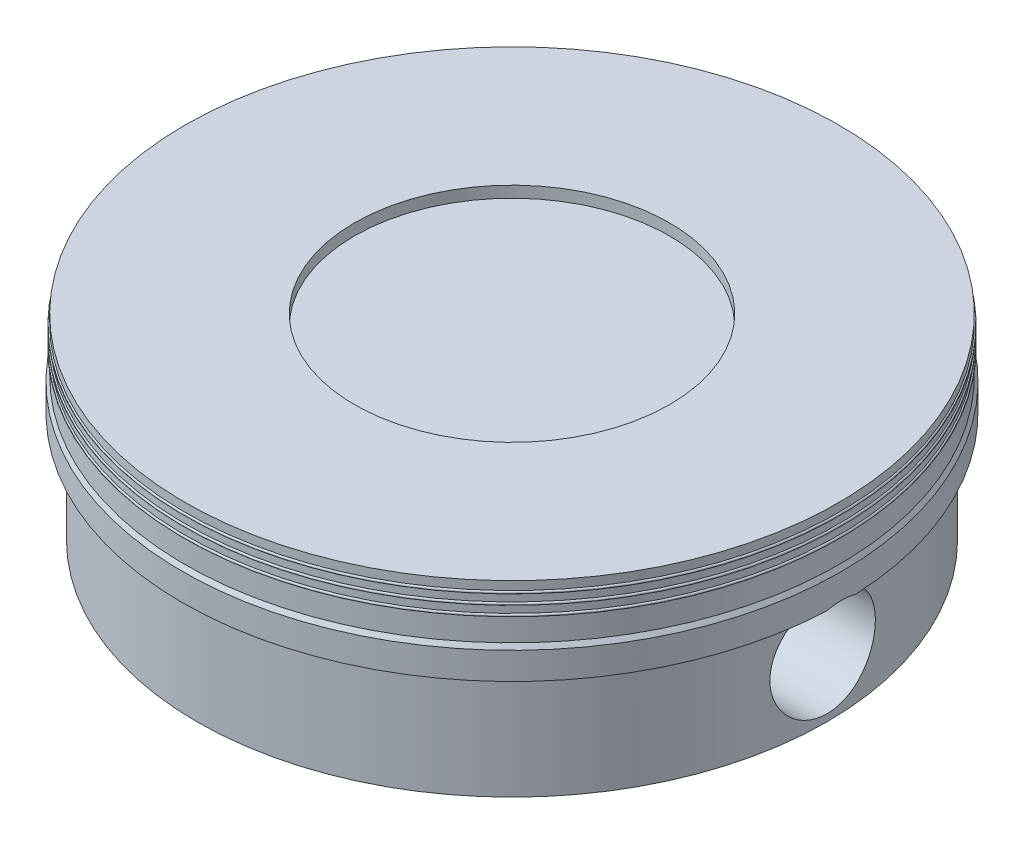
SolidWorks part; units mm, degrees
ref_plane "Front Plane" through (0, 0, 0) normal (0, 0, 1) x (1, 0, 0)
ref_plane "Top Plane" through (0, 0, 0) normal (0, 1, 0) x (1, 0, 0)
ref_plane "Right Plane" through (0, 0, 0) normal (1, 0, 0) x (0, 0, -1)
sketch "Sketch1" plane through (0, 0, 0) normal (0, 0, 1) x (1, 0, 0)
  line L0 (0, 3) -> (0, 0) construction
  line L1 (0, 0) -> (5, 0) construction
  line L2 (4.78, 0) -> (3.43, 0)
  line L3 (3.43, 0) -> (3.43, 1.93)
  line L4 (3.43, 1.93) -> (4.2, 1.93)
  line L5 (4.2, 1.93) -> (4.2, 2.33)
  line L6 (4.2, 2.33) -> (0, 2.33)
  line L7 (0, 2.33) -> (0, 2.8)
  line L8 (0, 2.8) -> (2.39, 2.8)
  line L9 (2.39, 2.8) -> (2.39, 2.972)
  line L10 (2.39, 2.972) -> (4.96, 2.972)
  line L11 (4.96, 2.972) -> (4.96, 2.842)
  line L12 (4.96, 2.155) -> (5, 2.085)
  line L13 (5, 2.085) -> (5, 1.675)
  line L14 (5, 1.675) -> (4.78, 1.675)
  line L15 (4.78, 1.675) -> (4.78, 0)
  line L16 (4.96, 2.802) -> (4.96, 2.692)
  line L17 (4.96, 2.652) -> (4.96, 2.542)
  line L18 (4.96, 2.502) -> (4.96, 2.155)
  arc A0 (4.96, 2.802) -> (4.96, 2.842) centre (4.96, 2.822) ccw
  arc A1 (4.96, 2.652) -> (4.96, 2.692) centre (4.96, 2.672) ccw
  arc A2 (4.96, 2.502) -> (4.96, 2.542) centre (4.96, 2.522) ccw
  point P22 (0, 0)
  point P23 (0, 0)
  dimension "D18" = 0.04
  dimension "D1" = 5
  dimension "D2" = 3
  dimension "D3" = 4.96
  dimension "D4" = 0.04
  dimension "D5" = 5
  dimension "D6" = 0.22
  dimension "D7" = 1.675
  dimension "D8" = 1.35
  dimension "D9" = 1.93
  dimension "D10" = 0.4
  dimension "D11" = 2.57
  dimension "D12" = 0.172
  dimension "D13" = 0.47
  dimension "D14" = 4.2
  dimension "D15" = 0.15
  dimension "D16" = 0.15
  dimension "D17" = 0.15
  dimension "D19" = 0.41
  dimension "D20" = 0.07
revolve "Revolve1" add sketch "Sketch1" angle 360 about L0
sketch "Sketch4" plane through (0, 0, 0) normal (0, -1, 0) x (1, 0, 0)
  line L1 (0, 0) -> (-3.43, 0) construction
  line L2 (-1.75, 2.95) -> (-1.75, -2.95)
  line L3 (1.75, 2.95) -> (1.75, -2.95)
  circle A0 centre (0, 0) radius 3.43 construction
  arc A1 (-1.75, 2.95) -> (-1.75, -2.95) centre (0, 0) ccw
  arc A2 (1.75, -2.95) -> (1.75, 2.95) centre (0, 0) ccw
  dimension "D1" = 3.5
extrude "Boss-Extrude2" add sketch "Sketch4" against normal blind 2.032 contours L2 A1 | L3 A2
sketch "Sketch5" plane through (0, 0, 0) normal (1, 0, 0) x (0, 0, -1)
  circle A0 centre (0, 0.9065) radius 0.8
  dimension "D1" = 1.6
  dimension "D2" = 0.9065
extrude "Cut-Extrude1" cut sketch "Sketch5" against normal through all both and the other way through all
